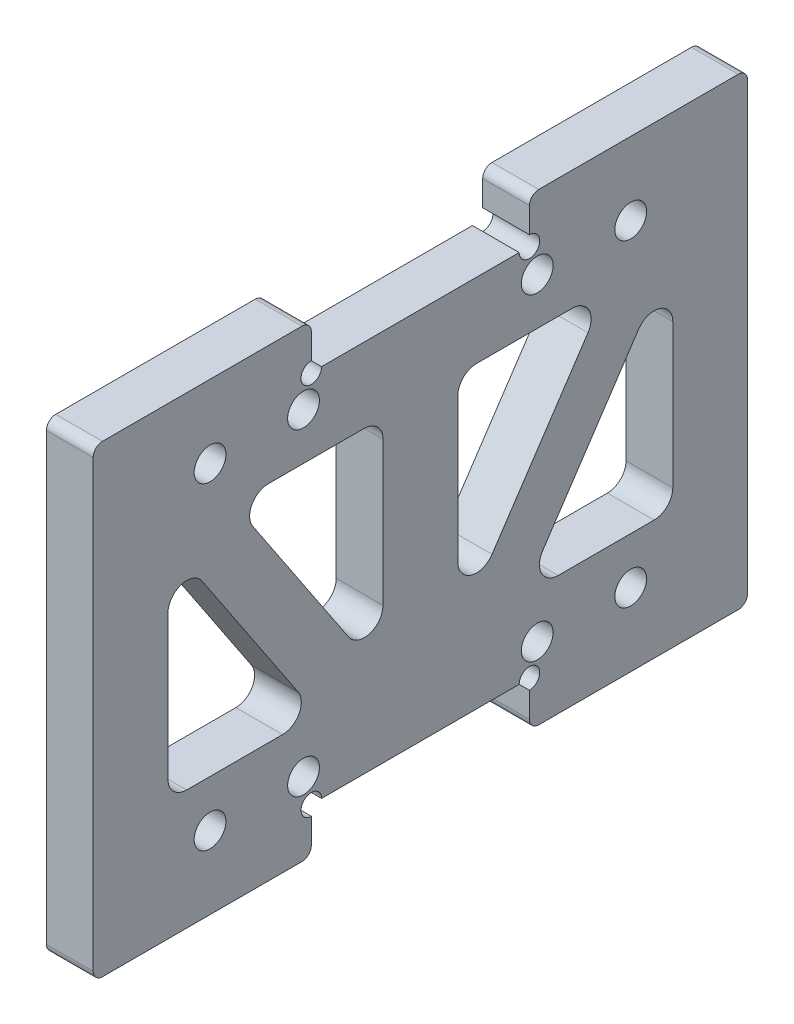
SolidWorks part; units mm, degrees
ref_plane "前视基准面" through (0, 0, 0) normal (0, 0, 1) x (1, 0, 0)
ref_plane "上视基准面" through (0, 0, 0) normal (0, 1, 0) x (1, 0, 0)
ref_plane "右视基准面" through (0, 0, 0) normal (1, 0, 0) x (0, 0, -1)
other "Configuration Table"
sketch "草图1" plane through (0, 0, 0) normal (1, 0, 0) x (0, 0, -1)
  line L1 (0, 0) -> (70, 0)
  line L2 (0, 0) -> (0, 40)
  line L3 (0, 40) -> (70, 40)
  line L4 (70, 0) -> (70, 40)
  dimension "D1" = 40
  dimension "D2" = 70
extrude "凸台-拉伸1" add sketch "草图1" along normal blind 5
sketch "草图2" plane through (5, 0, 0) normal (1, 0, 0) x (0, 0, -1)
  line L0 (62, 32) -> (62, 8)
  line L1 (39, 32) -> (39, 8)
  line L2 (55, 32) -> (39, 32)
  line L3 (39, 8) -> (55, 32)
  line L4 (8, 32) -> (24, 8)
  line L5 (31, 8) -> (15, 32)
  line L6 (15, 32) -> (31, 32)
  line L7 (31, 32) -> (31, 8)
  line L8 (8, 32) -> (8, 8)
  line L9 (8, 8) -> (62, 8)
  line L10 (62, 8) -> (62, 32)
  line L11 (62, 32) -> (8, 32)
  line L12 (8, 32) -> (8, 8)
  line L13 (8, 8) -> (62, 8)
  line L14 (62, 8) -> (62, 32)
  line L15 (62, 32) -> (8, 32)
  line L16 (35, 32) -> (35, 8) construction
  line L17 (62, 32) -> (46, 8)
  dimension "D2" = 4
  dimension "D3" = 16
  dimension "D1" = 8
extrude "切除-拉伸1" cut sketch "草图2" against normal blind 5 contours L12 L13 L4 | L7 L6 L5 | L1 L3 L2 | L0 L17 L13
fillet "圆角1" radius 2 12 edges at (2.5, 8, -46) (2.5, 8, -62) (2.5, 32, -62) (2.5, 32, -55) (2.5, 32, -39) (2.5, 8, -39) (2.5, 8, -31) (2.5, 32, -31) (2.5, 32, -15) (2.5, 8, -24) (2.5, 8, -8) (2.5, 32, -8)
sketch "草图3" plane through (5, 0, 0) normal (1, 0, 0) x (0, 0, -1)
  line L0 (23.3333, 44.8) -> (46.6667, 44.8) construction
  line L1 (0, 40) -> (23.3333, 40)
  line L2 (0, 40) -> (0, 44.8)
  line L3 (0, 44.8) -> (23.3333, 44.8)
  line L4 (23.3333, 40) -> (23.3333, 44.8)
  line L5 (70, 40) -> (46.6667, 40)
  line L6 (70, 40) -> (70, 44.8)
  line L7 (70, 44.8) -> (46.6667, 44.8)
  line L8 (46.6667, 40) -> (46.6667, 44.8)
  line L9 (0, 20) -> (70, 20) construction
  line L10 (0, 40) -> (0, 0) construction
  line L11 (70, 0) -> (70, 40) construction
  line L12 (23.3333, -4.8) -> (46.6667, -4.8) construction
  line L13 (46.6667, 0) -> (46.6667, -4.8)
  line L14 (70, -4.8) -> (46.6667, -4.8)
  line L15 (70, 0) -> (70, -4.8)
  line L16 (70, 0) -> (46.6667, 0)
  line L17 (23.3333, 0) -> (23.3333, -4.8)
  line L18 (0, -4.8) -> (23.3333, -4.8)
  line L19 (0, 0) -> (0, -4.8)
  line L20 (0, 0) -> (23.3333, 0)
  dimension "D1" = 4.8
extrude "凸台-拉伸2" add sketch "草图3" against normal blind 5
fillet "圆角2" radius 1 8 edges at (2.5, -4.8, -70) (2.5, -4.8, -46.6667) (2.5, -4.8, -23.3333) (2.5, -4.8, 0) (2.5, 44.8, -70) (2.5, 44.8, -46.6667) (2.5, 44.8, -23.3333) (2.5, 44.8, 0)
sketch "草图4" plane through (5, 0, 0) normal (1, 0, 0) x (0, 0, -1)
  circle A0 centre (23.3333, 40) radius 1.1
  circle A1 centre (46.6667, 40) radius 1.1
  circle A2 centre (46.6667, 0) radius 1.1
  circle A3 centre (23.3333, 0) radius 1.1
  dimension "D1" = 2.2
extrude "切除-拉伸2" cut sketch "草图4" against normal blind 5
hole_wizard "M3 间隙孔1" positions "草图5" profile "草图6" hole size "M3" standard "GB" end condition through all
sketch "草图5" plane through (5, 0, 0) normal (1, 0, 0) x (0, 0, -1)
  line L0 (35, 40) -> (35, 0) construction
  line L1 (45.5667, 40) -> (24.4333, 40) construction
  line L2 (24.4333, 0) -> (45.5667, 0) construction
  point P0 (57.5, 37)
  point P3 (47.5, 37)
  point P6 (57.5, 3)
  point P9 (47.5, 3)
  point P21 (22.5, 3)
  point P22 (12.5, 3)
  point P23 (22.5, 37)
  point P24 (12.5, 37)
sketch "草图6" plane through (5, 37, -57.5) normal (0, 1, 0) x (0, 0, -1)
  line L0 (0, 0) -> (0, 5)
  line L1 (0, 5) -> (1.7, 5)
  line L2 (1.7, 5) -> (1.7, 0)
  line L5 (1.7, 0) -> (0, 0)
  line L11 (0, -6.35) -> (0, 107.95) construction
  dimension "通孔孔直径" = 3.4
  dimension "通孔孔深度" = 5
